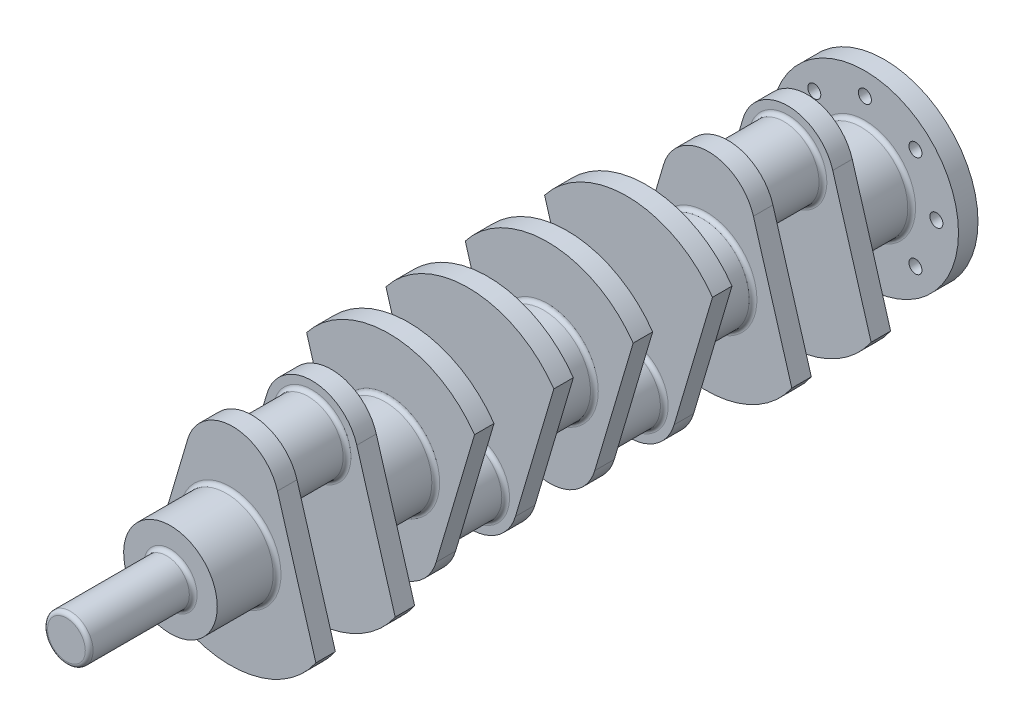
SolidWorks part; units mm, degrees
ref_plane "Front Plane" through (0, 0, 0) normal (0, 0, 1) x (1, 0, 0)
ref_plane "Top Plane" through (0, 0, 0) normal (0, 1, 0) x (1, 0, 0)
ref_plane "Right Plane" through (0, 0, 0) normal (1, 0, 0) x (0, 0, -1)
sketch "Sketch1" plane through (0, 0, 0) normal (0, 0, 1) x (1, 0, 0)
  line L0 (-32.7446, -54.2246) -> (-63.298, 48.922)
  line L1 (36.2905, -54.2246) -> (65.8214, 45.4702)
  circle A0 centre (1.7729, -44) radius 36
  arc A1 (-63.298, 48.922) -> (65.8214, 45.4702) centre (0, 0) cw
  dimension "D1" = 72
  dimension "D3" = 44
  dimension "D4" = 80
  dimension "D2" = 33
  dimension "D5" = 0
extrude "Boss-Extrude1" add sketch "Sketch1" along normal blind 15
sketch "Sketch3" plane through (0, 0, 0) normal (0, 0, -1) x (-1, 0, 0)
  circle A0 centre (-1.7729, -44) radius 27
  dimension "D1" = 54
extrude "Boss-Extrude2" add sketch "Sketch3" along normal blind 46
sketch "Sketch5" plane through (0, 0, 15) normal (0, 0, 1) x (1, 0, 0)
  circle A0 centre (0, 0) radius 36
  dimension "D1" = 72
extrude "Boss-Extrude3" add sketch "Sketch5" along normal blind 46
ref_plane "Plane1" through (0, 0, -23) normal (0, 0, -1) x (-1, 0, 0)
mirror "Mirror1" about plane through (0, 0, -23) normal (0, 0, -1) of bodies 103
ref_plane "Plane2" through (0, 0, -84) normal (0, 0, -1) x (-1, 0, 0)
mirror "Mirror2" about plane through (0, 0, -84) normal (0, 0, -1) of bodies 104
move or copy body "Body-Move/Copy1" bodies to move or copy 105 copy no rotation origin (0, 0, -145) rotation axis (1, 0, 0) rotation angle 180
ref_plane "Plane3" through (0, 0, 38) normal (0, 0, 1) x (1, 0, 0)
mirror "Mirror3" about plane through (0, 0, 38) normal (0, 0, 1) of bodies 106 104
sketch "Sketch7" plane through (0, 0, 305) normal (0, 0, 1) x (1, 0, 0)
  circle A0 centre (0, 0) radius 17.5
  dimension "D1" = 35
extrude "Boss-Extrude4" add sketch "Sketch7" along normal blind 80
sketch "Sketch8" plane through (0, 0, -229) normal (0, 0, -1) x (-1, 0, 0)
  circle A0 centre (0, 0) radius 72
  circle A1 centre (0, 0) radius 55
  circle A2 centre (0, 55) radius 5
  circle A3 centre (38.8909, 38.8909) radius 5
  circle A4 centre (55, 0) radius 5
  circle A5 centre (38.8909, -38.8909) radius 5
  circle A6 centre (0, -55) radius 5
  circle A7 centre (-38.8909, -38.8909) radius 5
  circle A8 centre (-55, 0) radius 5
  circle A9 centre (-38.8909, 38.8909) radius 5
  point P22 (0, 0)
  circle M11 centre (0, 0) radius 36
  dimension "D1" = 144
  dimension "D2" = 110
  dimension "D3" = 10
  dimension "D4" = 8
extrude "Boss-Extrude6" add sketch "Sketch8" along normal blind 15 contours A0 A9 A1 A2 A3 A4 A5 A6 A7 A8 | A9 A1 A8 A7 A6 A5 A4 A3 A2 M11 | M11
combine bodies "Combine1" operation type add bodies to combine 111 104 108 109
fillet "Fillet1" radius 3 19 edges at (28.7729, 44, -122) (-25.2271, 44, -168) (36, 0, -107) (36, 0, -183) (36, 0, -229) (28.7729, -44, 0) (36, 0, 15) (36, 0, -61) (-25.2271, -44, -46) (36, 0, 61) (28.7729, -44, 76) (-25.2271, -44, 122) (36, 0, 137) (36, 0, 183) (28.7729, 44, 198) (36, 0, 259) (-25.2271, 44, 244) (17.5, 0, 305) (17.5, 0, 385)
